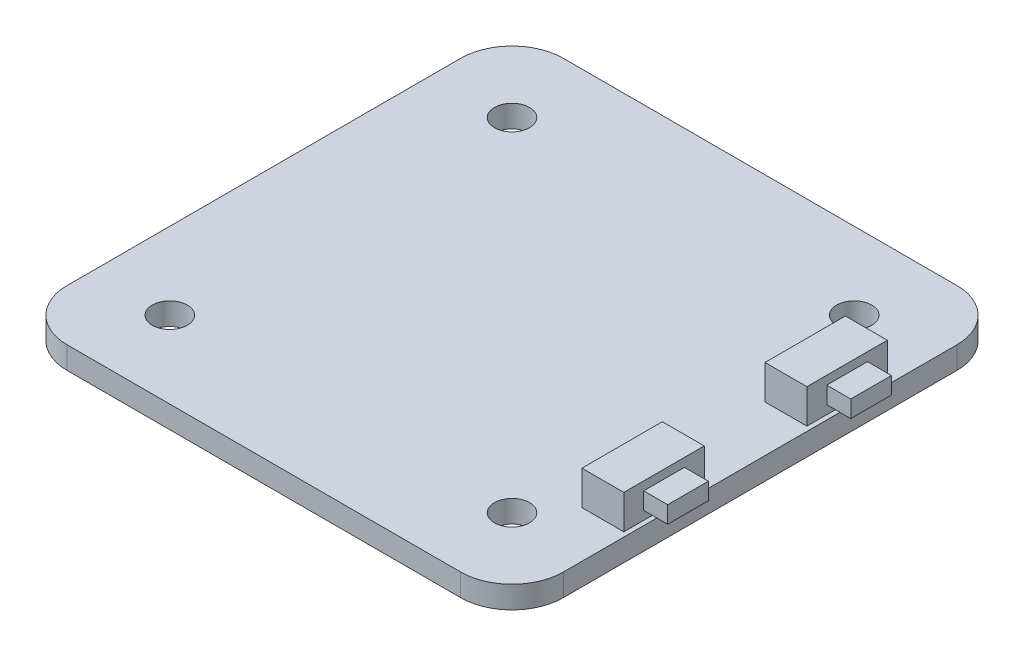
SolidWorks part; units mm, degrees
ref_plane "Front Plane" through (0, 0, 0) normal (0, 0, 1) x (1, 0, 0)
ref_plane "Top Plane" through (0, 0, 0) normal (0, 1, 0) x (1, 0, 0)
ref_plane "Right Plane" through (0, 0, 0) normal (1, 0, 0) x (0, 0, -1)
sketch "Sketch1" plane through (0, 0, 0) normal (0, 1, 0) x (1, 0, 0)
  line L0 (14.5, 29) -> (14.5, 0) construction
  line L1 (3, 0) -> (26, 0)
  line L2 (0, 3) -> (0, 26)
  line L3 (3, 29) -> (26, 29)
  line L4 (29, 3) -> (29, 26)
  line L5 (0, 14.5) -> (29, 14.5) construction
  line L7 (4.5, 24.5) -> (24.5, 24.5) construction
  line L8 (4.5, 24.5) -> (4.5, 4.5) construction
  line L9 (4.5, 4.5) -> (24.5, 4.5) construction
  line L10 (24.5, 24.5) -> (24.5, 4.5) construction
  arc A0 (26, 29) -> (29, 26) centre (26, 26) cw
  arc A1 (26, 0) -> (29, 3) centre (26, 3) ccw
  arc A2 (3, 0) -> (0, 3) centre (3, 3) cw
  arc A3 (0, 26) -> (3, 29) centre (3, 26) cw
  circle A4 centre (4.5, 24.5) radius 1.025
  circle A6 centre (24.5, 24.5) radius 1.025
  circle A7 centre (24.5, 4.5) radius 1.025
  circle A8 centre (4.5, 4.5) radius 1.025
  point P7 (29, 29)
  point P12 (0, 0)
  point P15 (0, 29)
  dimension "D2" = 3
  dimension "D3" = 2.05
  dimension "D1" = 29
  dimension "D4" = 20
  dimension "D5" = 2
  dimension "D6" = 2
extrude "Boss-Extrude1" add sketch "Sketch1" along normal blind 1.3
sketch "Sketch2" plane through (0, 1.3, 0) normal (0, 1, 0) x (1, 0, 0)
  line L0 (29, 14.5) -> (0, 14.5) construction
  line L1 (29, 3) -> (29, 26) construction
  line L2 (0, 26) -> (0, 3) construction
  line L3 (26, 29) -> (3, 29) construction
  line L4 (28.737, 22.2) -> (26.287, 22.2)
  line L5 (28.737, 22.2) -> (28.737, 17.5)
  line L6 (28.737, 17.5) -> (26.287, 17.5)
  line L7 (26.287, 22.2) -> (26.287, 17.5)
  line L8 (26.287, 6.8) -> (26.287, 11.5)
  line L9 (28.737, 11.5) -> (26.287, 11.5)
  line L10 (28.737, 6.8) -> (28.737, 11.5)
  line L11 (28.737, 6.8) -> (26.287, 6.8)
  dimension "D1" = 4.7
  dimension "D2" = 11.5
  dimension "D3" = 2.45
extrude "Boss-Extrude2" add sketch "Sketch2" along normal blind 2
sketch "Sketch3" plane through (28.737, 0, 0) normal (1, 0, 0) x (0, 0, -1)
  line L0 (14.5, 1.3) -> (14.5, 3.3233) construction
  line L1 (3, 1.3) -> (26, 1.3) construction
  line L2 (6.8, 2.3) -> (11.5, 2.3) construction
  line L3 (7.9609, 2.7957) -> (10.3391, 2.7957)
  line L4 (7.9609, 2.7957) -> (7.9609, 1.8043)
  line L5 (7.9609, 1.8043) -> (10.3391, 1.8043)
  line L6 (10.3391, 2.7957) -> (10.3391, 1.8043)
  line L7 (6.8, 3.3) -> (6.8, 1.3) construction
  line L8 (11.5, 3.3) -> (11.5, 1.3) construction
  line L9 (9.15, 3.3) -> (9.15, 1.3) construction
  line L10 (6.8, 3.3) -> (11.5, 3.3) construction
  line L11 (18.6609, 2.7957) -> (18.6609, 1.8043)
  line L12 (21.0391, 1.8043) -> (18.6609, 1.8043)
  line L13 (21.0391, 2.7957) -> (21.0391, 1.8043)
  line L14 (21.0391, 2.7957) -> (18.6609, 2.7957)
extrude "Boss-Extrude3" add sketch "Sketch3" along normal blind 1.4
